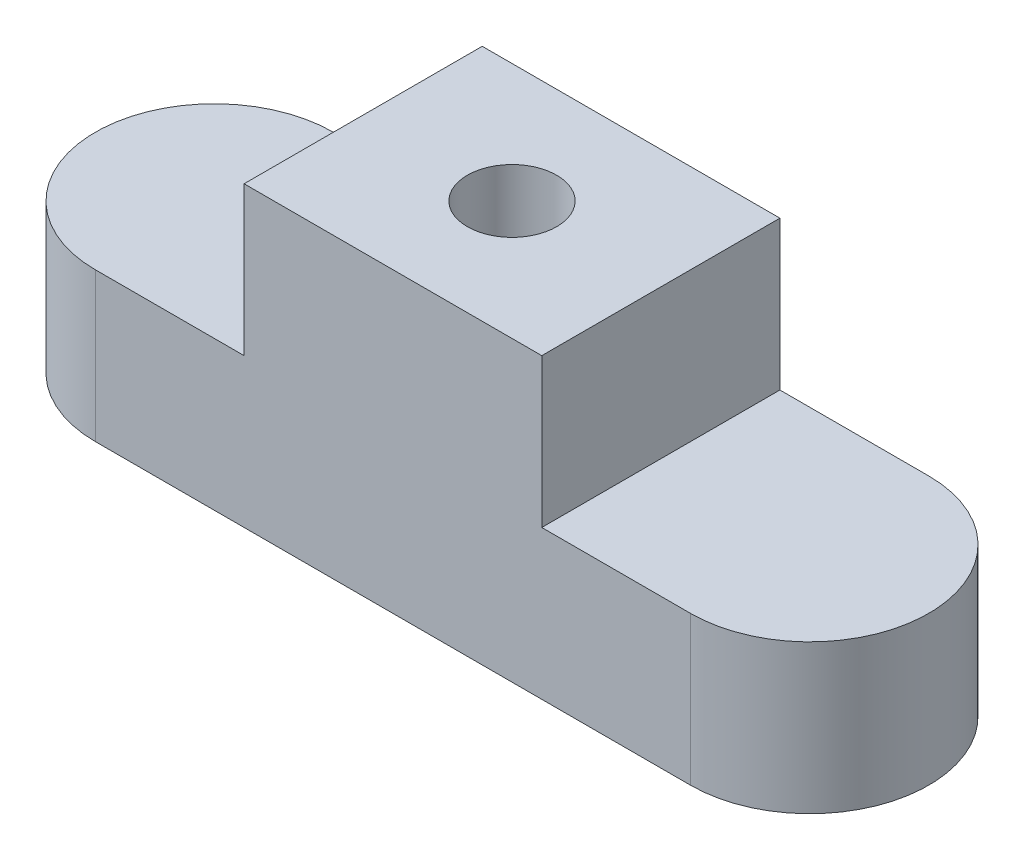
SolidWorks part; units mm, degrees
ref_plane "Front Plane" through (0, 0, 0) normal (0, 0, 1) x (1, 0, 0)
ref_plane "Top Plane" through (0, 0, 0) normal (0, 1, 0) x (1, 0, 0)
ref_plane "Right Plane" through (0, 0, 0) normal (1, 0, 0) x (0, 0, -1)
sketch "Sketch1" plane through (0, 0, 0) normal (0, 1, 0) x (1, 0, 0)
  line L1 (10, -4) -> (-10, -4)
  line L3 (10, 4) -> (-10, 4)
  line L5 (10, -4) -> (-10, 4) construction
  line L6 (10, 4) -> (-10, -4) construction
  arc A0 (-10, 4) -> (-10, -4) centre (-10, 0) ccw
  arc A1 (10, -4) -> (10, 4) centre (10, 0) ccw
  point P0 (0, 0)
  dimension "D1" = 8
  dimension "D2" = 20
extrude "Boss-Extrude1" add sketch "Sketch1" along normal blind 5
sketch "Sketch2" plane through (0, 5, 0) normal (0, 1, 0) x (1, 0, 0)
  line L0 (10, 4) -> (-10, 4) construction
  line L1 (5, -4) -> (-5, -4)
  line L2 (5, -4) -> (5, 4)
  line L3 (5, 4) -> (-5, 4)
  line L4 (-5, -4) -> (-5, 4)
  line L5 (5, -4) -> (-5, 4) construction
  line L6 (5, 4) -> (-5, -4) construction
  point P0 (0, 0)
  dimension "D1" = 10
extrude "Boss-Extrude2" add sketch "Sketch2" along normal blind 5
sketch "Sketch3" plane through (0, 10, 0) normal (0, 1, 0) x (1, 0, 0)
  circle A0 centre (0, 0) radius 1.5
  dimension "D1" = 3
extrude "Cut-Extrude1" cut sketch "Sketch3" against normal blind 8
